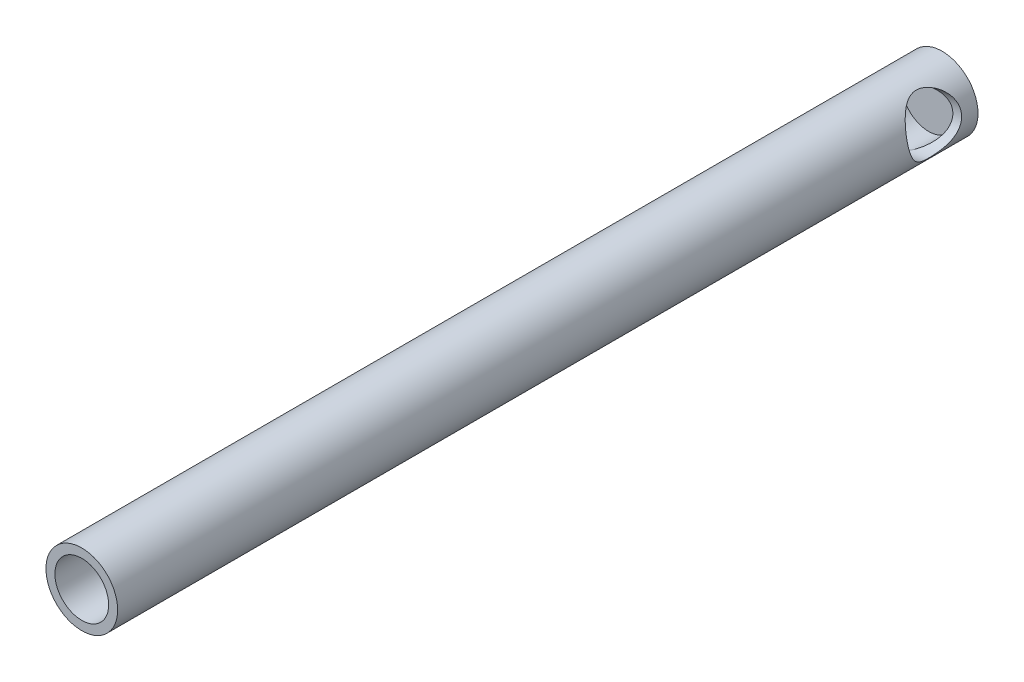
SolidWorks part; units mm, degrees
ref_plane "Front" through (0, 0, 0) normal (0, 0, 1) x (1, 0, 0)
ref_plane "Top" through (0, 0, 0) normal (0, 1, 0) x (1, 0, 0)
ref_plane "Right" through (0, 0, 0) normal (1, 0, 0) x (0, 0, -1)
sketch "Sketch1" plane through (0, 0, 0) normal (0, 0, 1) x (1, 0, 0)
  circle A0 centre (0, 0) radius 3.175
extrude "Boss-Extrude1" add sketch "Sketch1" along normal blind 76.2
sketch "Sketch5" plane through (0, 0, 76.2) normal (0, 0, 1) x (1, 0, 0)
  circle A0 centre (0, 0) radius 2.3813
extrude "Cut-Extrude3" cut sketch "Sketch5" against normal blind 75
hole_wizard "3/16 (0.1875) Diameter Hole2" positions "3DSketch2" profile "Sketch6" hole size "3/16" standard "ANSI Inch"
sketch3d "3DSketch2"
  point P0 (3.0835, 0.7569, 3.7787)
sketch "Sketch6" plane through (3.0835, 0.7569, 3.7787) normal (0, 0, 1) x (-0.2384, 0.9712, 0)
  line L0 (0, 0) -> (0, 0.7937)
  line L1 (0, 0.7937) -> (2.3812, 0.7937)
  line L2 (2.3812, 0.7937) -> (2.3812, 0)
  line L5 (2.3812, 0) -> (0, 0)
  line L11 (0, -6.35) -> (0, 107.95) construction
  dimension "Thru Hole Dia." = 4.7625
  dimension "Thru Hole Depth" = 0.7937
